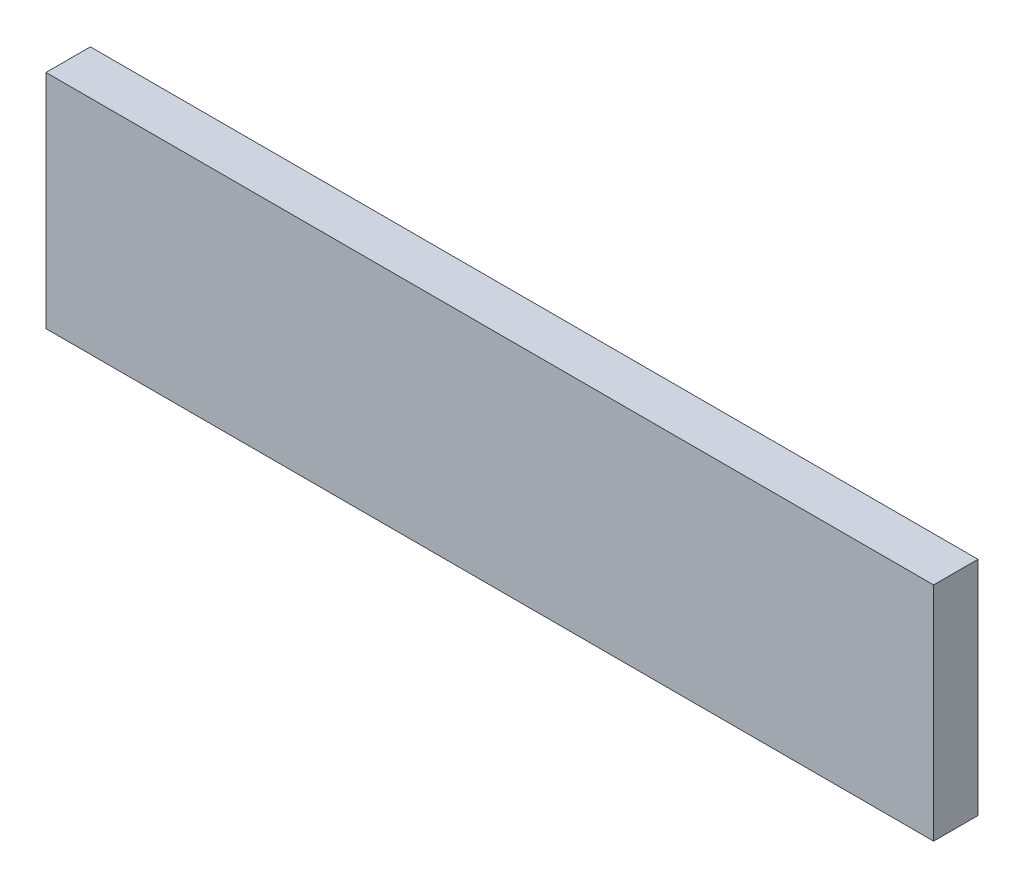
SolidWorks part; units mm, degrees
ref_plane "Front Plane" through (0, 0, 0) normal (0, 0, 1) x (1, 0, 0)
ref_plane "Top Plane" through (0, 0, 0) normal (0, 1, 0) x (1, 0, 0)
ref_plane "Right Plane" through (0, 0, 0) normal (1, 0, 0) x (0, 0, -1)
sketch "Sketch1" plane through (0, 0, 0) normal (0, 0, 1) x (1, 0, 0)
  line L1 (-63.5, -15.875) -> (63.5, -15.875)
  line L2 (-63.5, -15.875) -> (-63.5, 15.875)
  line L3 (-63.5, 15.875) -> (63.5, 15.875)
  line L4 (63.5, -15.875) -> (63.5, 15.875)
  line L5 (-63.5, -15.875) -> (63.5, 15.875) construction
  line L6 (-63.5, 15.875) -> (63.5, -15.875) construction
  point P0 (0, 0)
extrude "Boss-Extrude1" add sketch "Sketch1" along normal blind 6.35
